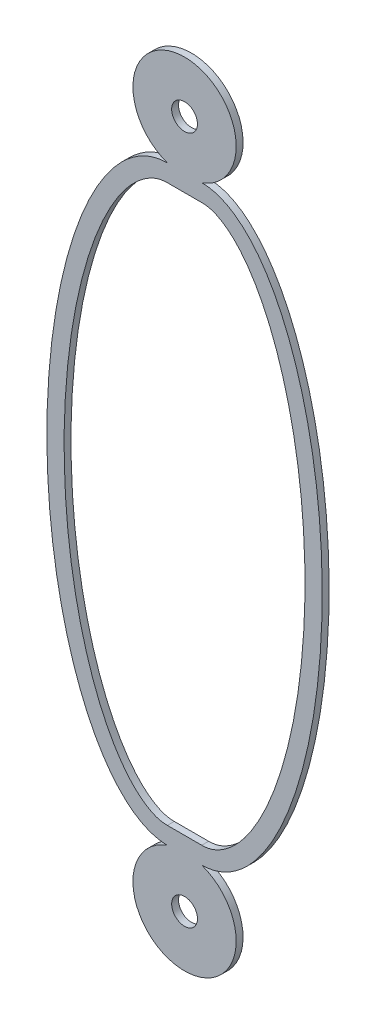
SolidWorks part; units mm, degrees
material "3.0517 (EN-AW 3003)"
ref_plane "Front Plane" through (0, 0, 0) normal (0, 0, 1) x (1, 0, 0)
ref_plane "Top Plane" through (0, 0, 0) normal (0, 1, 0) x (1, 0, 0)
ref_plane "Right Plane" through (0, 0, 0) normal (1, 0, 0) x (0, 0, -1)
sketch "Sketch1" plane through (0, 0, 0) normal (0, 0, 1) x (1, 0, 0)
  line L0 (0, 10) -> (0, -10) construction
  line L1 (-0.5, 8.5858) -> (-0.5, -8.5858) construction
  line L2 (0.5, 8.5858) -> (0.5, -8.5858) construction
  line L3 (-0.5, 10) -> (-0.5, -10) construction
  line L4 (0.5, 10) -> (0.5, -10) construction
  line L5 (0, 10) -> (0, -10) construction
  line L6 (-0.5, 8.5858) -> (0.5, 8.5858) construction
  line L7 (-4, 0) -> (4, 0) construction
  line L8 (-0.5, 8.0858) -> (0.5, 8.0858)
  line L9 (-0.5, -8.0858) -> (0.5, -8.0858)
  circle A0 centre (0, 10) radius 0.375
  arc A1 (0.5, 8.5858) -> (-0.5, 8.5858) centre (0, 10) ccw
  arc A2 (-0.5, -8.5858) -> (0.5, -8.5858) centre (0, -10) ccw
  circle A3 centre (0, -10) radius 0.375
  ellipse E0 centre (-0.5, 0) end of major axis (-0.5, 8.5858) minor radius 3.5 (-0.5, 8.5858) -> (-0.5, -8.5858) ccw
  ellipse E1 centre (0.5, 0) end of major axis (0.5, 8.5858) minor radius 3.5 (0.5, 8.5858) -> (0.5, -8.5858) cw
  spline S0 degree 1 poles (-0.5, 8.0858) (-0.5, -8.0858) knots 0 0 1 1 construction
  spline S1 degree 3 poles (-0.5, 8.0858) (-0.6591, 8.0858) (-0.9459, 8.0184) (-1.4819, 7.6358) (-2.0246, 6.9277) (-2.6926, 5.5895) (-3.3219, 3.2913) (-3.589, 0) (-3.3219, -3.2913) (-2.6926, -5.5895) (-2.0246, -6.9277) (-1.4819, -7.6358) (-0.9459, -8.0184) (-0.6591, -8.0858) (-0.5, -8.0858) knots 0 0 0 0 0.19635 0.392699 0.589049 0.785398 1.178097 1.570796 1.963495 2.356194 2.552544 2.748894 2.945243 3.141593 3.141593 3.141593 3.141593
  spline S2 degree 1 poles (0.5, 8.0858) (0.5, -8.0858) knots 0 0 1 1 construction
  spline S3 degree 3 poles (0.5, 8.0858) (0.6591, 8.0858) (0.9459, 8.0184) (1.4819, 7.6358) (2.0246, 6.9277) (2.6926, 5.5895) (3.3219, 3.2913) (3.589, 0) (3.3219, -3.2913) (2.6926, -5.5895) (2.0246, -6.9277) (1.4819, -7.6358) (0.9459, -8.0184) (0.6591, -8.0858) (0.5, -8.0858) knots -3.141593 -3.141593 -3.141593 -3.141593 -2.945243 -2.748894 -2.552544 -2.356194 -1.963495 -1.570796 -1.178097 -0.785398 -0.589049 -0.392699 -0.19635 0 0 0 0
  dimension "D2" = 0.75
  dimension "D3" = 3
  dimension "D4" = 0.5
  dimension "D5" = 0.5
  dimension "D1" = 20
  dimension "D6" = 8
  dimension "D7" = 0.5
  dimension "D8" = 0.5
extrude "Boss-Extrude1" add sketch "Sketch1" along normal mid plane 0.2
sketch "Sketch2" plane through (0, 0, 0) normal (0, 0, 1) x (1, 0, 0)
  line L2 (-0.5, -8.8358) -> (0.5, -8.8358)
  line L3 (-0.5, 8.8358) -> (0.5, 8.8358)
  line L4 (-0.5, -7.8358) -> (0.5, -7.8358)
  line L5 (0.5, 7.8358) -> (-0.5, 7.8358)
  line L6 (-0.5, -7.8358) -> (0.5, -7.8358)
  line L7 (0.5, 7.8358) -> (-0.5, 7.8358)
  spline S0 degree 3 poles (-2229.1949, -1991.2485) (72.937, -173.3882) (13.4796, 15.8535) (-1.5474, 8.5211) (-1.7897, 8.3391) (-2.4733, 7.6445) (-2.8738, 6.9813) (-3.539, 5.3496) (-3.8022, 4.3806) (-4.1579, 2.274) (-4.25, 1.1372) (-4.25, -1.1372) (-4.1579, -2.274) (-3.8022, -4.3806) (-3.539, -5.3496) (-2.8738, -6.9813) (-2.4733, -7.6445) (-1.7897, -8.3391) (-1.5474, -8.5211) (13.4795, -15.8535) (72.9366, 173.3869) (-2229.1709, 1991.2296) knots -3.55864 -3.55864 -3.55864 -3.55864 0.0625 0.0625 0.125 0.125 0.25 0.25 0.375 0.375 0.5 0.5 0.625 0.625 0.75 0.75 0.875 0.875 0.9375 0.9375 4.558627 4.558627 4.558627 4.558627 only from (-0.5, 8.8358) to (-0.5, -8.8358)
  spline S1 degree 3 poles (-0.5, 8.8358) (-0.7692, 8.8358) (-1.0375, 8.7699) (-1.5474, 8.5211) (-1.7897, 8.3391) (-2.4733, 7.6445) (-2.8738, 6.9813) (-3.539, 5.3496) (-3.8022, 4.3806) (-4.1579, 2.274) (-4.25, 1.1372) (-4.25, -1.1372) (-4.1579, -2.274) (-3.8022, -4.3806) (-3.539, -5.3496) (-2.8738, -6.9813) (-2.4733, -7.6445) (-1.7897, -8.3391) (-1.5474, -8.5211) (-1.0375, -8.7699) (-0.7692, -8.8358) (-0.5, -8.8358) knots 0 0 0 0 0.0625 0.0625 0.125 0.125 0.25 0.25 0.375 0.375 0.5 0.5 0.625 0.625 0.75 0.75 0.875 0.875 0.9375 0.9375 1 1 1 1
  spline S2 degree 3 poles (2229.1949, 1991.2485) (-72.937, 173.3882) (-13.4796, -15.8535) (1.5474, -8.5211) (1.7897, -8.3391) (2.4733, -7.6445) (2.8738, -6.9813) (3.539, -5.3496) (3.8022, -4.3806) (4.1579, -2.274) (4.25, -1.1372) (4.25, 1.1372) (4.1579, 2.274) (3.8022, 4.3806) (3.539, 5.3496) (2.8738, 6.9813) (2.4733, 7.6445) (1.7897, 8.3391) (1.5474, 8.5211) (-13.4795, 15.8535) (-72.9366, -173.3869) (2229.1709, -1991.2296) knots -3.55864 -3.55864 -3.55864 -3.55864 0.0625 0.0625 0.125 0.125 0.25 0.25 0.375 0.375 0.5 0.5 0.625 0.625 0.75 0.75 0.875 0.875 0.9375 0.9375 4.558627 4.558627 4.558627 4.558627 only from (0.5, -8.8358) to (0.5, 8.8358)
  spline S3 degree 3 poles (0.5, -8.8358) (0.7692, -8.8358) (1.0375, -8.7699) (1.5474, -8.5211) (1.7897, -8.3391) (2.4733, -7.6445) (2.8738, -6.9813) (3.539, -5.3496) (3.8022, -4.3806) (4.1579, -2.274) (4.25, -1.1372) (4.25, 1.1372) (4.1579, 2.274) (3.8022, 4.3806) (3.539, 5.3496) (2.8738, 6.9813) (2.4733, 7.6445) (1.7897, 8.3391) (1.5474, 8.5211) (1.0375, 8.7699) (0.7692, 8.8358) (0.5, 8.8358) knots 0 0 0 0 0.0625 0.0625 0.125 0.125 0.25 0.25 0.375 0.375 0.5 0.5 0.625 0.625 0.75 0.75 0.875 0.875 0.9375 0.9375 1 1 1 1
  spline S8 degree 3 poles (2525.5997, 1592.0681) (-84.5926, 249.192) (-10.0925, -12.0725) (0.8573, -7.7501) (0.9371, -7.7041) (1.1657, -7.5481) (1.3001, -7.4196) (1.5407, -7.143) (1.6493, -6.9924) (1.8468, -6.6839) (1.9359, -6.5252) (2.1834, -6.0396) (2.3217, -5.7033) (2.5634, -5.0145) (2.6663, -4.6625) (2.9313, -3.605) (3.0519, -2.8915) (3.2113, -1.4519) (3.2502, -0.7227) (3.2498, 0.7318) (3.2111, 1.4543) (3.0522, 2.8892) (2.932, 3.6017) (2.6671, 4.6599) (2.5641, 5.0122) (2.3219, 5.703) (2.1819, 6.0432) (1.9327, 6.5311) (1.8432, 6.6899) (1.6462, 6.9969) (1.5382, 7.1462) (1.2968, 7.4231) (1.1618, 7.5512) (0.9353, 7.7051) (0.8562, 7.7506) (-9.112, 11.674) (-75.5846, -203.7982) (2634.4505, -1412.1828) knots -1.943296 -1.943296 -1.943296 -1.943296 0.015625 0.015625 0.03125 0.03125 0.0625 0.0625 0.09375 0.09375 0.125 0.125 0.1875 0.1875 0.25 0.25 0.375 0.375 0.5 0.5 0.625 0.625 0.75 0.75 0.8125 0.8125 0.875 0.875 0.90625 0.90625 0.9375 0.9375 0.96875 0.96875 0.984375 0.984375 2.773996 2.773996 2.773996 2.773996 only from (0.5, -7.8358) to (0.5, 7.8358)
  spline S9 degree 3 poles (-2525.5997, -1592.0681) (84.5926, -249.192) (10.0925, 12.0725) (-0.8573, 7.7501) (-0.9371, 7.7041) (-1.1657, 7.5481) (-1.3001, 7.4196) (-1.5407, 7.143) (-1.6493, 6.9924) (-1.8468, 6.6839) (-1.9359, 6.5252) (-2.1834, 6.0396) (-2.3217, 5.7033) (-2.5634, 5.0145) (-2.6663, 4.6625) (-2.9313, 3.605) (-3.0519, 2.8915) (-3.2113, 1.4519) (-3.2502, 0.7227) (-3.2498, -0.7318) (-3.2111, -1.4543) (-3.0522, -2.8892) (-2.932, -3.6017) (-2.6671, -4.6599) (-2.5641, -5.0122) (-2.3219, -5.703) (-2.1819, -6.0432) (-1.9327, -6.5311) (-1.8432, -6.6899) (-1.6462, -6.9969) (-1.5382, -7.1462) (-1.2968, -7.4231) (-1.1618, -7.5512) (-0.9353, -7.7051) (-0.8562, -7.7506) (9.112, -11.674) (75.5846, 203.7982) (-2634.4505, 1412.1828) knots -1.943296 -1.943296 -1.943296 -1.943296 0.015625 0.015625 0.03125 0.03125 0.0625 0.0625 0.09375 0.09375 0.125 0.125 0.1875 0.1875 0.25 0.25 0.375 0.375 0.5 0.5 0.625 0.625 0.75 0.75 0.8125 0.8125 0.875 0.875 0.90625 0.90625 0.9375 0.9375 0.96875 0.96875 0.984375 0.984375 2.773996 2.773996 2.773996 2.773996 only from (-0.5, 7.8358) to (-0.5, -7.8358)
  spline S10 degree 3 poles (0.5, -7.8358) (0.5934, -7.8358) (0.684, -7.8185) (0.8573, -7.7501) (0.9371, -7.7041) (1.1657, -7.5481) (1.3001, -7.4196) (1.5407, -7.143) (1.6493, -6.9924) (1.8468, -6.6839) (1.9359, -6.5252) (2.1834, -6.0396) (2.3217, -5.7033) (2.5634, -5.0145) (2.6663, -4.6625) (2.9313, -3.605) (3.0519, -2.8915) (3.2113, -1.4519) (3.2502, -0.7227) (3.2498, 0.7318) (3.2111, 1.4543) (3.0522, 2.8892) (2.932, 3.6017) (2.6671, 4.6599) (2.5641, 5.0122) (2.3219, 5.703) (2.1819, 6.0432) (1.9327, 6.5311) (1.8432, 6.6899) (1.6462, 6.9969) (1.5382, 7.1462) (1.2968, 7.4231) (1.1618, 7.5512) (0.9353, 7.7051) (0.8562, 7.7506) (0.6836, 7.8185) (0.593, 7.8358) (0.5, 7.8358) knots 0 0 0 0 0.015625 0.015625 0.03125 0.03125 0.0625 0.0625 0.09375 0.09375 0.125 0.125 0.1875 0.1875 0.25 0.25 0.375 0.375 0.5 0.5 0.625 0.625 0.75 0.75 0.8125 0.8125 0.875 0.875 0.90625 0.90625 0.9375 0.9375 0.96875 0.96875 0.984375 0.984375 1 1 1 1
  spline S11 degree 3 poles (-0.5, 7.8358) (-0.5934, 7.8358) (-0.684, 7.8185) (-0.8573, 7.7501) (-0.9371, 7.7041) (-1.1657, 7.5481) (-1.3001, 7.4196) (-1.5407, 7.143) (-1.6493, 6.9924) (-1.8468, 6.6839) (-1.9359, 6.5252) (-2.1834, 6.0396) (-2.3217, 5.7033) (-2.5634, 5.0145) (-2.6663, 4.6625) (-2.9313, 3.605) (-3.0519, 2.8915) (-3.2113, 1.4519) (-3.2502, 0.7227) (-3.2498, -0.7318) (-3.2111, -1.4543) (-3.0522, -2.8892) (-2.932, -3.6017) (-2.6671, -4.6599) (-2.5641, -5.0122) (-2.3219, -5.703) (-2.1819, -6.0432) (-1.9327, -6.5311) (-1.8432, -6.6899) (-1.6462, -6.9969) (-1.5382, -7.1462) (-1.2968, -7.4231) (-1.1618, -7.5512) (-0.9353, -7.7051) (-0.8562, -7.7506) (-0.6836, -7.8185) (-0.593, -7.8358) (-0.5, -7.8358) knots 0 0 0 0 0.015625 0.015625 0.03125 0.03125 0.0625 0.0625 0.09375 0.09375 0.125 0.125 0.1875 0.1875 0.25 0.25 0.375 0.375 0.5 0.5 0.625 0.625 0.75 0.75 0.8125 0.8125 0.875 0.875 0.90625 0.90625 0.9375 0.9375 0.96875 0.96875 0.984375 0.984375 1 1 1 1
  dimension "D1" = 0.25
  dimension "D2" = 0.25
  dimension "D3" = 0.25
extrude "Boss-Extrude2" [suppressed] add sketch "Sketch2" along normal mid plane 0.6
